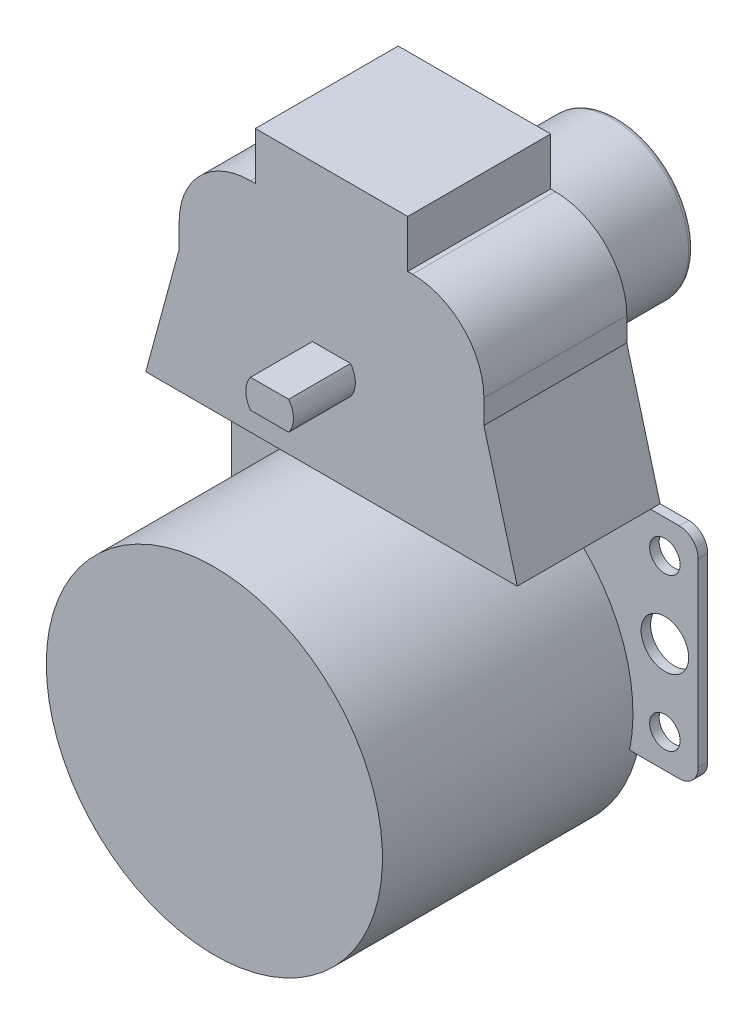
SolidWorks part; units mm, degrees
ref_plane "Front Plane" through (0, 0, 0) normal (0, 0, 1) x (1, 0, 0)
ref_plane "Top Plane" through (0, 0, 0) normal (0, 1, 0) x (1, 0, 0)
ref_plane "Right Plane" through (0, 0, 0) normal (1, 0, 0) x (0, 0, -1)
sketch "Sketch1" plane through (0, 0, 0) normal (0, 0, 1) x (1, 0, 0)
  circle A0 centre (0, 0) radius 8
  dimension "D1" = 16
extrude "Boss-Extrude1" add sketch "Sketch1" along normal blind 13
sketch "Sketch2" plane through (0, 0, 13) normal (0, 0, 1) x (1, 0, 0)
  circle A0 centre (0, 0) radius 8.75
  dimension "D1" = 17.5
extrude "Boss-Extrude2" add sketch "Sketch2" along normal blind 2
sketch "Sketch3" plane through (0, 0, 15) normal (0, 0, 1) x (1, 0, 0)
  line L1 (-24.5, 17.87) -> (24.5, 17.87)
  line L2 (-24.5, 17.87) -> (-24.5, -44.63)
  line L3 (-24.5, -44.63) -> (24.5, -44.63)
  line L4 (24.5, 17.87) -> (24.5, -44.63)
  circle A0 centre (0, 0) radius 8.75 construction
  dimension "D4" = 17.87
  dimension "D1" = 49
  dimension "D2" = 24.5
  dimension "D3" = 62.5
extrude "Boss-Extrude3" add sketch "Sketch3" along normal blind 15
sketch "Sketch4" plane through (0, 0, 15) normal (0, 0, -1) x (-1, 0, 0)
  circle A0 centre (0, -29.5) radius 17.65
  circle A1 centre (0, 0) radius 8 construction
  dimension "D1" = 29.5
  dimension "D2" = 35.3
extrude "Boss-Extrude4" add sketch "Sketch4" against normal blind 27.3
sketch "Sketch6" plane through (0, 0, 0) normal (0, 0, -1) x (-1, 0, 0)
  line L0 (-2, 1.5) -> (2, 1.5)
  line L1 (-2, -1.5) -> (2, -1.5)
  circle A0 centre (0, 0) radius 2.5
  dimension "D1" = 5
  dimension "D2" = 3
  dimension "D3" = 1.5
extrude "Boss-Extrude6" add sketch "Sketch6" against normal blind 36.5 contours L0 A0 L1
sketch "Sketch7" plane through (0, 0, 30) normal (0, 0, 1) x (1, 0, 0)
  line L0 (-8, 17.87) -> (8, 17.87)
  line L1 (24.5, 17.87) -> (-24.5, 17.87) construction
  line L2 (8, 17.87) -> (8, 12.87)
  line L3 (8, 12.87) -> (8.5, 12.87)
  line L4 (16, 5.37) -> (16, 2.87)
  line L5 (16, 2.87) -> (19.5, -10)
  line L6 (19.5, -10) -> (22.5, -10)
  line L7 (24.5, -12) -> (24.5, -31)
  line L8 (22.5, -33) -> (17.2995, -33)
  line L9 (24.5, -44.63) -> (24.5, 17.87) construction
  line L10 (0, -29.5) -> (0, 0) construction
  line L11 (-22.5, -33) -> (-17.2995, -33)
  line L12 (-24.5, -12) -> (-24.5, -31)
  line L13 (-19.5, -10) -> (-22.5, -10)
  line L14 (-16, 2.87) -> (-19.5, -10)
  line L15 (-16, 5.37) -> (-16, 2.87)
  line L16 (-8, 12.87) -> (-8.5, 12.87)
  line L17 (-8, 17.87) -> (-8, 12.87)
  line L19 (-39.6823, 27.5253) -> (41.4284, 27.5253)
  line L20 (-39.6823, 27.5253) -> (-39.6823, -54.9352)
  line L21 (-39.6823, -54.9352) -> (41.4284, -54.9352)
  line L22 (41.4284, 27.5253) -> (41.4284, -54.9352)
  circle A0 centre (0, -29.5) radius 17.65 construction
  arc A1 (17.2995, -33) -> (-17.2995, -33) centre (0, -29.5) cw
  arc A3 (8.5, 12.87) -> (16, 5.37) centre (8.5, 5.37) cw
  arc A4 (-16, 5.37) -> (-8.5, 12.87) centre (-8.5, 5.37) cw
  arc A5 (22.5, -10) -> (24.5, -12) centre (22.5, -12) cw
  arc A6 (24.5, -31) -> (22.5, -33) centre (22.5, -31) cw
  arc A7 (-22.5, -33) -> (-24.5, -31) centre (-22.5, -31) cw
  arc A8 (-24.5, -12) -> (-22.5, -10) centre (-22.5, -12) cw
  point P31 (16, 12.87)
  point P34 (-16, 12.87)
  point P37 (24.5, -10)
  point P40 (24.5, -33)
  point P43 (-24.5, -33)
  point P46 (-24.5, -10)
  dimension "D2" = 7.5
  dimension "D10" = 2
  dimension "D1" = 8
  dimension "D3" = 5
  dimension "D4" = 8
  dimension "D5" = 10
  dimension "D6" = 5
  dimension "D7" = 23
  dimension "D8" = 0
  dimension "D9" = 27.87
extrude "Cut-Extrude1" cut sketch "Sketch7" against normal through all
sketch "Sketch8" plane through (0, 0, 30) normal (0, 0, 1) x (1, 0, 0)
  line L4 (0, 0) -> (0, -29.5) construction
  line L9 (-17.2995, -33) -> (-22.5, -33)
  line L10 (-24.5, -31) -> (-24.5, -12)
  line L11 (-22.5, -10) -> (22.5, -10)
  line L12 (24.5, -31) -> (24.5, -12)
  line L13 (17.2995, -33) -> (22.5, -33)
  arc A9 (-22.5, -33) -> (-24.5, -31) centre (-22.5, -31) cw
  arc A10 (-24.5, -31) -> (-22.5, -33) centre (-22.5, -31) ccw construction
  arc A11 (-24.5, -12) -> (-22.5, -10) centre (-22.5, -12) cw
  arc A12 (-17.2995, -33) -> (17.2995, -33) centre (0, -29.5) cw
  arc A14 (24.5, -12) -> (22.5, -10) centre (22.5, -12) ccw
  arc A15 (22.5, -33) -> (24.5, -31) centre (22.5, -31) ccw
  point P31 (0, -10)
extrude "Cut-Extrude2" cut sketch "Sketch8" against normal blind 14
sketch "Sketch9" plane through (0, 0, 16) normal (0, 0, 1) x (1, 0, 0)
  line L0 (-24.5, -12) -> (-24.5, -31) construction
  line L1 (-24.5, -21.5) -> (24.5, -21.5) construction
  line L2 (24.5, -31) -> (24.5, -12) construction
  circle A3 centre (-21, -21.5) radius 2.5
  circle A4 centre (21, -21.5) radius 2.5
  circle A6 centre (0, -29.5) radius 17.65 construction
  dimension "D1" = 42
  dimension "D2" = 5
  dimension "D3" = 21
  dimension "D4" = 5
sketch "Sketch10" plane through (0, 0, 16) normal (0, 0, 1) x (1, 0, 0)
  circle A0 centre (-21, -13.5) radius 1.6
  circle A1 centre (21, -13.5) radius 1.6
  circle A2 centre (21, -29.5) radius 1.6
  circle A3 centre (-21, -29.5) radius 1.6
  circle A5 centre (0, 0) radius 3.628 construction
  circle A6 centre (-21, -21.5) radius 2.5 construction
  dimension "D1" = 3.2
  dimension "D2" = 3.2
  dimension "D3" = 3.2
  dimension "D4" = 3.2
  dimension "D5" = 42
  dimension "D6" = 16
  dimension "D7" = 8
  dimension "D8" = 13.5
  dimension "D9" = 0
  dimension "D10" = 16
extrude "Cut-Extrude4" cut sketch "Sketch9" against normal through all
extrude "Cut-Extrude5" cut sketch "Sketch10" against normal through all
fillet "Fillet1" radius 0.5 1 edges at (8, 0, 0)
sketch "Sketch11" plane through (0, 0, 0) normal (0, 0, -1) x (-1, 0, 0)
  line L1 (-3, 1.05) -> (3, 1.05)
  line L2 (-3, 1.05) -> (-3, -1.05)
  line L3 (-3, -1.05) -> (3, -1.05)
  line L4 (3, 1.05) -> (3, -1.05)
  dimension "D1" = 6
  dimension "D2" = 2.1
  dimension "D3" = 3
  dimension "D4" = 1.05
extrude "Cut-Extrude6" cut sketch "Sketch11" against normal blind 12
